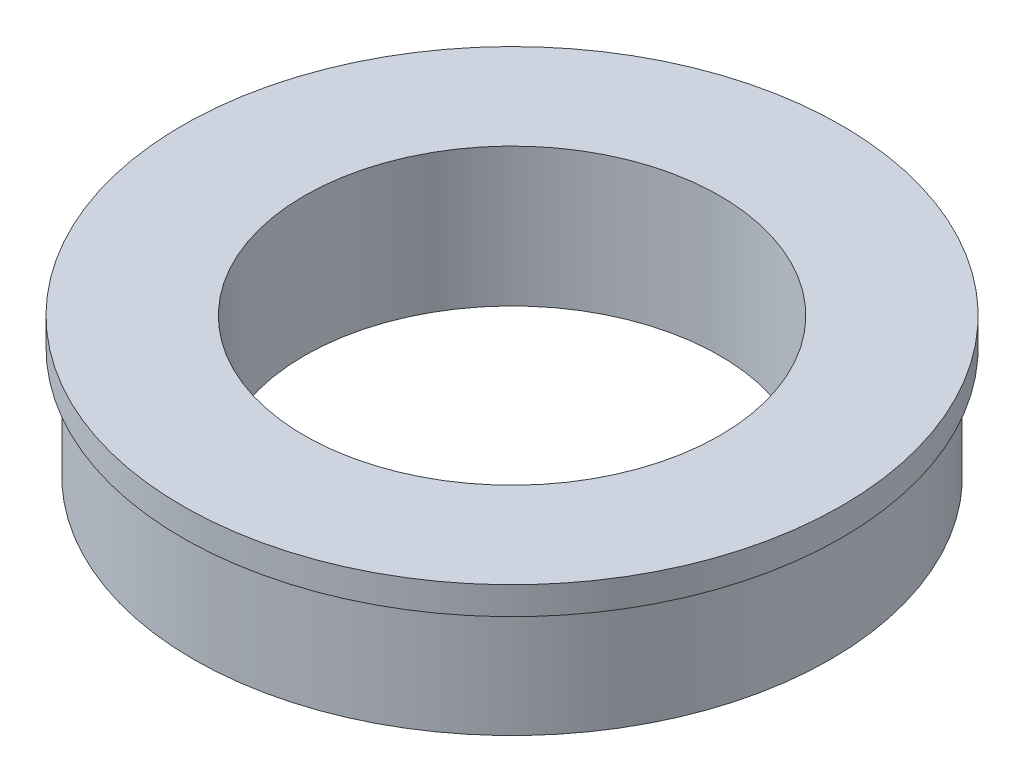
SolidWorks part; units mm, degrees
ref_plane "Front Plane" through (0, 0, 0) normal (0, 0, 1) x (1, 0, 0)
ref_plane "Top Plane" through (0, 0, 0) normal (0, 1, 0) x (1, 0, 0)
ref_plane "Right Plane" through (0, 0, 0) normal (1, 0, 0) x (0, 0, -1)
sketch "Sketch2" plane through (0, 0, 0) normal (0, 0, 1) x (1, 0, 0)
  line L0 (0, -19.423) -> (0, 19.423) construction
  line L1 (4.7625, 9.9553) -> (4.7625, 6.7803)
  line L2 (4.7625, 6.7803) -> (7.3025, 6.7803)
  line L3 (7.3025, 6.7803) -> (7.3025, 9.3203)
  line L4 (7.3025, 9.3203) -> (7.5565, 9.3203)
  line L5 (7.5565, 9.3203) -> (7.5565, 9.9553)
  line L6 (7.5565, 9.9553) -> (4.7625, 9.9553)
  point P4 (0, 0)
  dimension "D1" = 9.525
  dimension "D2" = 2.54
  dimension "D3" = 0.635
  dimension "D4" = 2.794
  dimension "D5" = 2.54
revolve "Revolve1" add sketch "Sketch2" angle 360 about L0
